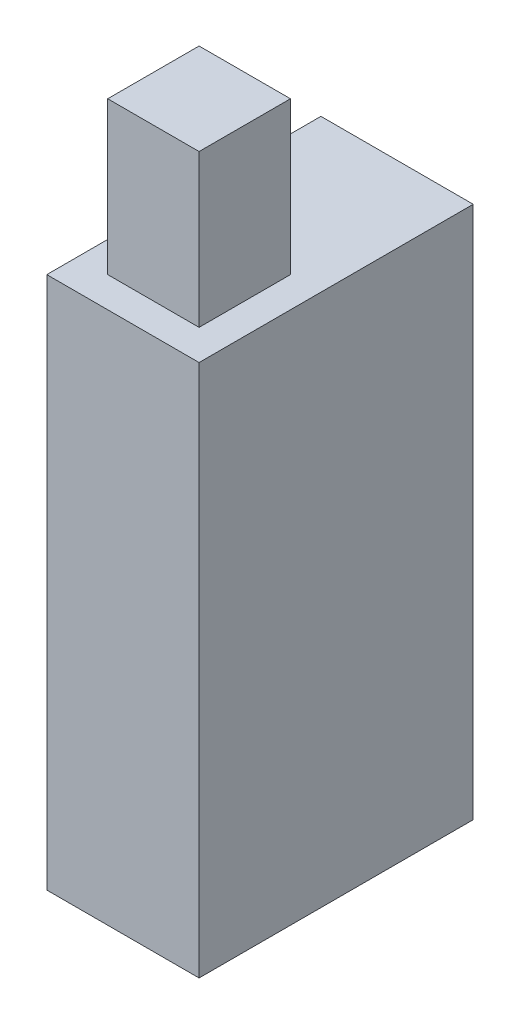
SolidWorks part; units mm, degrees
ref_plane "Front Plane" through (0, 0, 0) normal (0, 0, 1) x (1, 0, 0)
ref_plane "Top Plane" through (0, 0, 0) normal (0, 1, 0) x (1, 0, 0)
ref_plane "Right Plane" through (0, 0, 0) normal (1, 0, 0) x (0, 0, -1)
sketch "Sketch1" plane through (0, 0, 0) normal (0, 1, 0) x (1, 0, 0)
  line L1 (-10, -18) -> (10, -18)
  line L2 (-10, -18) -> (-10, 18)
  line L3 (-10, 18) -> (10, 18)
  line L4 (10, -18) -> (10, 18)
  line L5 (-10, -18) -> (10, 18) construction
  line L6 (-10, 18) -> (10, -18) construction
  point P0 (0, 0)
  dimension "D1" = 20
  dimension "D2" = 36
extrude "Boss-Extrude1" add sketch "Sketch1" along normal blind 70
sketch "Sketch2" plane through (0, 70, 0) normal (0, 1, 0) x (1, 0, 0)
  line L0 (-10, -18) -> (10, -18) construction
  line L1 (-6, -14) -> (6, -14)
  line L2 (-6, -14) -> (-6, -2)
  line L3 (-6, -2) -> (6, -2)
  line L4 (6, -14) -> (6, -2)
  line L5 (-6, -14) -> (6, -2) construction
  line L6 (-6, -2) -> (6, -14) construction
  point P0 (0, -8)
  point P7 (0, 0)
  point P8 (0, -18)
  dimension "D1" = 12
  dimension "D2" = 12
  dimension "D3" = 10
extrude "Boss-Extrude2" add sketch "Sketch2" along normal blind 20
